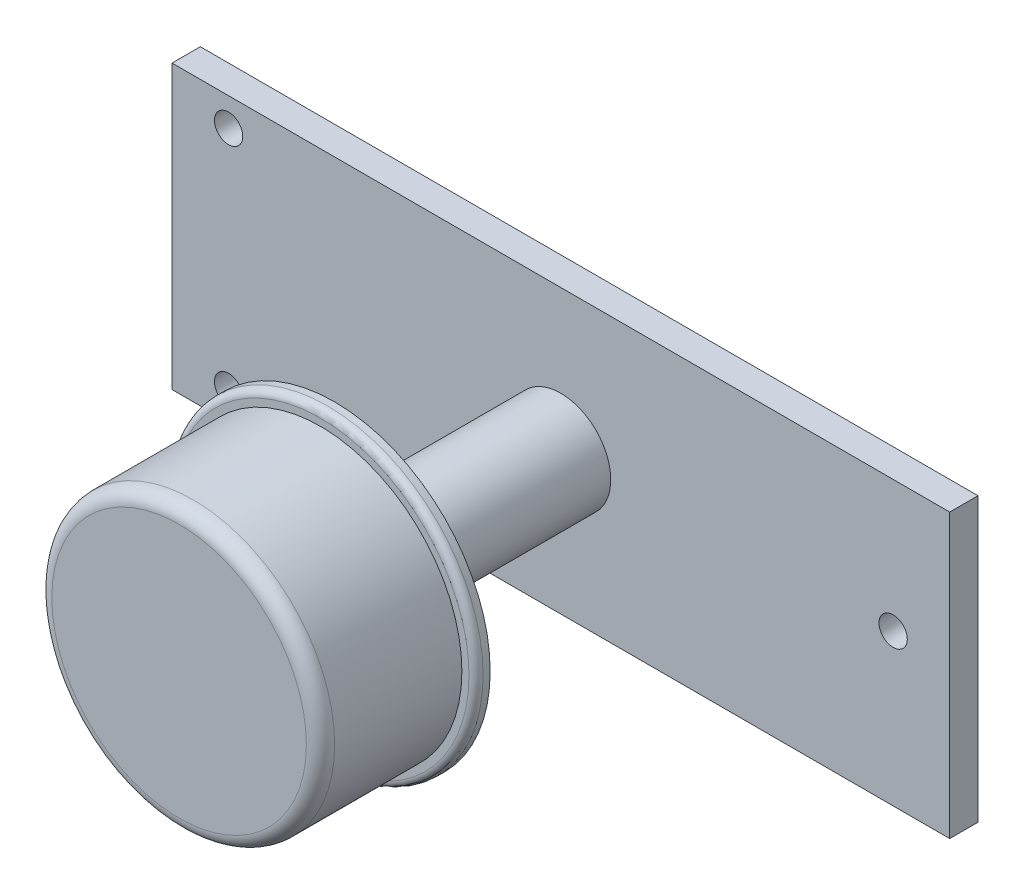
SolidWorks part; units mm, degrees
ref_plane "Front Plane" through (0, 0, 0) normal (0, 0, 1) x (1, 0, 0)
ref_plane "Top Plane" through (0, 0, 0) normal (0, 1, 0) x (1, 0, 0)
ref_plane "Right Plane" through (0, 0, 0) normal (1, 0, 0) x (0, 0, -1)
sketch "Sketch1" plane through (0, 0, 0) normal (0, 0, 1) x (1, 0, 0)
  line L1 (0, 0) -> (55, 0)
  line L2 (0, 0) -> (0, 20)
  line L3 (0, 20) -> (55, 20)
  line L4 (55, 0) -> (55, 20)
  circle A0 centre (4, 18) radius 1
  circle A1 centre (4, 2) radius 1
  circle A2 centre (51, 10.7109) radius 1
  dimension "D7" = 2
  dimension "D8" = 2
  dimension "D9" = 2
  dimension "D1" = 20
  dimension "D2" = 55
  dimension "D3" = 47
  dimension "D4" = 4
  dimension "D5" = 2
  dimension "D6" = 2
extrude "Boss-Extrude1" add sketch "Sketch1" along normal blind 2
sketch "Sketch2" plane through (0, 0, 2) normal (0, 0, 1) x (1, 0, 0)
  line L0 (55, 20) -> (0, 20) construction
  line L1 (55, 0) -> (55, 20) construction
  circle A0 centre (27.5, 10) radius 3.5266
  point P5 (27.5, 20)
  point P8 (55, 10)
extrude "Boss-Extrude2" add sketch "Sketch2" along normal blind 16
sketch "Sketch3" plane through (0, 0, 18) normal (0, 0, 1) x (1, 0, 0)
  circle A0 centre (27.5, 10) radius 11
  dimension "D1" = 22
extrude "Boss-Extrude3" add sketch "Sketch3" along normal blind 1
sketch "Sketch5" plane through (0, 0, 19) normal (0, 0, 1) x (1, 0, 0)
  circle A0 centre (27.5, 10) radius 10
extrude "Boss-Extrude4" add sketch "Sketch5" along normal blind 10
fillet "Fillet1" radius 1 1 edges at (37.5, 10, 29)
fillet "Fillet2" radius 0.5 1 edges at (38.5, 10, 19)
